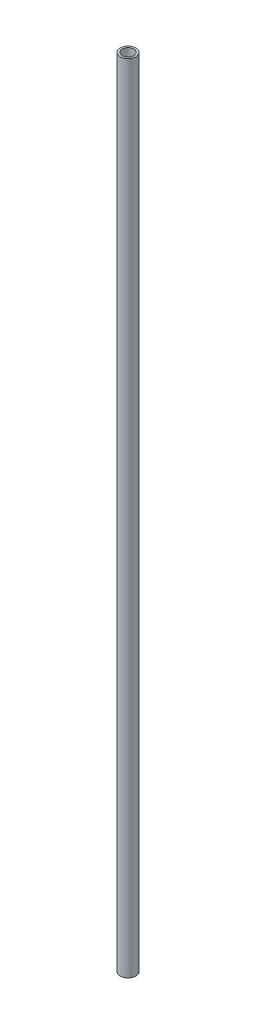
SolidWorks part; units mm, degrees
ref_plane "Front Plane" through (0, 0, 0) normal (0, 0, 1) x (1, 0, 0)
ref_plane "Top Plane" through (0, 0, 0) normal (0, 1, 0) x (1, 0, 0)
ref_plane "Right Plane" through (0, 0, 0) normal (1, 0, 0) x (0, 0, -1)
sketch "Sketch1" plane through (0, 0, 0) normal (0, 1, 0) x (1, 0, 0)
  circle A0 centre (0, 0) radius 19.5
  circle A1 centre (0, 0) radius 14.5
  dimension "D1" = 39
  dimension "D2" = 5
extrude "Boss-Extrude1" add sketch "Sketch1" along normal blind 2000
